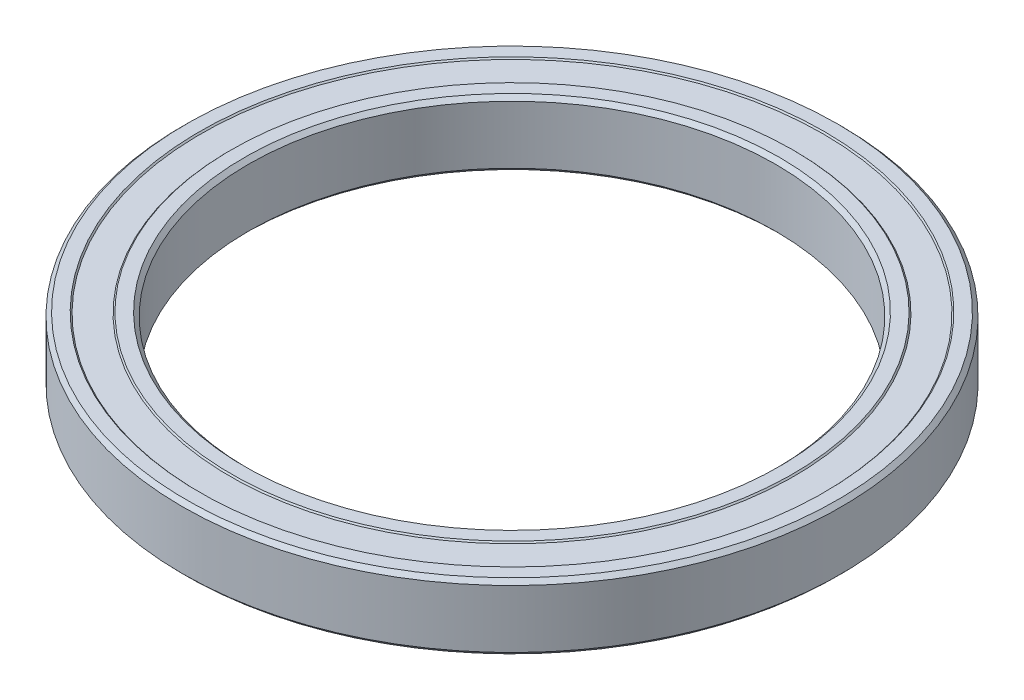
SolidWorks part; units mm, degrees
material "Stainless Steel (ferritic)"
ref_plane "Front Plane" through (0, 0, 0) normal (0, 0, 1) x (1, 0, 0)
ref_plane "Top Plane" through (0, 0, 0) normal (0, 1, 0) x (1, 0, 0)
ref_plane "Right Plane" through (0, 0, 0) normal (1, 0, 0) x (0, 0, -1)
sketch "Sketch1" plane through (0, 0, 0) normal (0, 0, 1) x (1, 0, 0)
  line L0 (0, -1.3494) -> (0, 70.5256) construction
  line L1 (40, 4.4) -> (40, -4.4)
  line L2 (40, -4.4) -> (40.6, -5)
  line L3 (40.6, -5) -> (42.6, -5)
  line L4 (42.6, -5) -> (42.8, -4.8)
  line L5 (42.8, -4.8) -> (47.2, -4.8)
  line L6 (47.2, -4.8) -> (47.4, -5)
  line L7 (47.4, -5) -> (49.4, -5)
  line L8 (49.4, -5) -> (50, -4.4)
  line L9 (50, -4.4) -> (50, 4.4)
  line L10 (50, 4.4) -> (49.4, 5)
  line L11 (49.4, 5) -> (47.4, 5)
  line L12 (47.4, 5) -> (47.2, 4.8)
  line L13 (47.2, 4.8) -> (42.8, 4.8)
  line L14 (42.8, 4.8) -> (42.6, 5)
  line L15 (42.6, 5) -> (40.6, 5)
  line L16 (40.6, 5) -> (40, 4.4)
  line L17 (0, 0) -> (40, 0) construction
  dimension "D1" = 40
  dimension "D2" = 10
  dimension "D3" = 0.6
  dimension "D4" = 0.2
  dimension "D5" = 50
  dimension "D6" = 2
revolve "Revolve1" add sketch "Sketch1" angle 360 about L0
